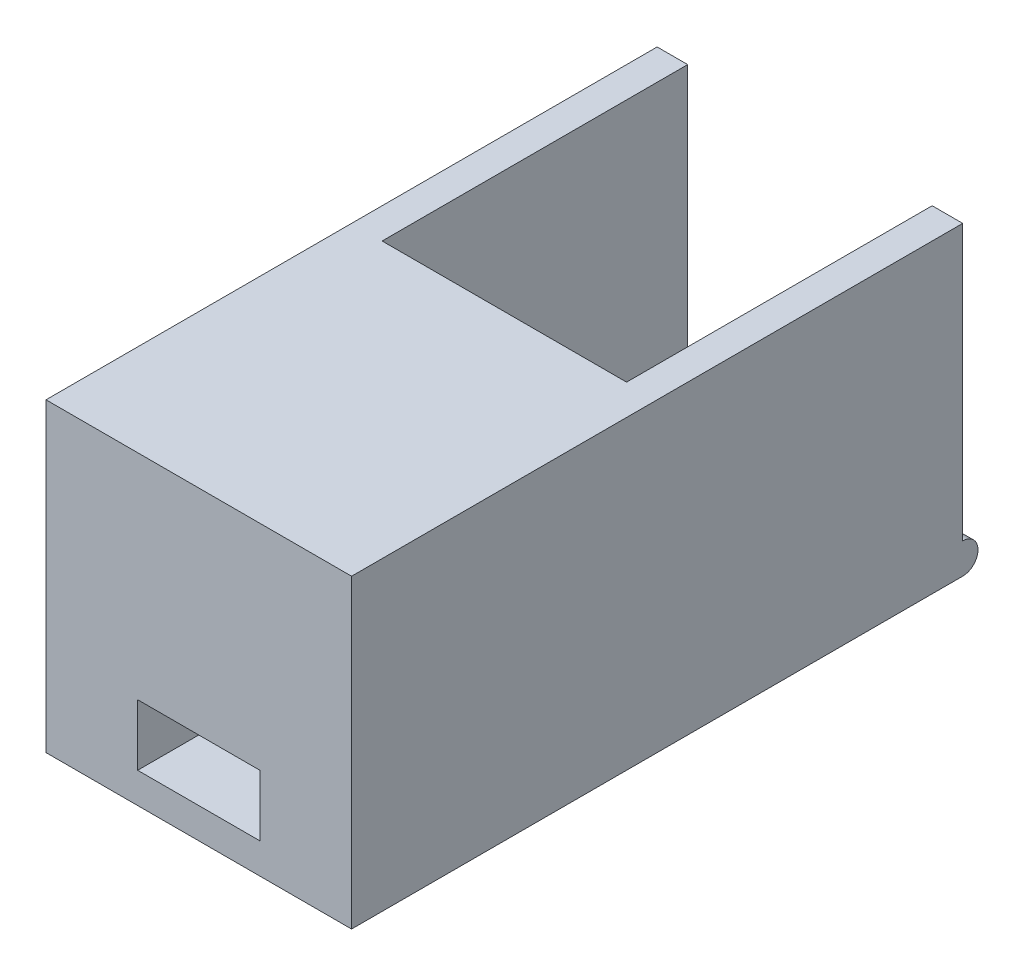
SolidWorks part; units mm, degrees
ref_plane "Front" through (0, 0, 0) normal (0, 0, 1) x (1, 0, 0)
ref_plane "Top" through (0, 0, 0) normal (0, 1, 0) x (1, 0, 0)
ref_plane "Right" through (0, 0, 0) normal (1, 0, 0) x (0, 0, -1)
sketch "草图1" plane through (0, 0, 0) normal (0, 1, 0) x (1, 0, 0)
  line L1 (-10, 20) -> (10, 20)
  line L2 (-10, 20) -> (-10, -20)
  line L3 (-10, -20) -> (10, -20)
  line L4 (10, 20) -> (10, -20)
  dimension "D1" = 40
  dimension "D2" = 20
  dimension "D3" = 10
  dimension "D4" = 20
extrude "凸台-拉伸1" add sketch "草图1" along normal blind 20
sketch "草图2" plane through (0, 20, 0) normal (0, 1, 0) x (1, 0, 0)
  line L0 (10, 20) -> (-10, 20) construction
  line L1 (-8, 20) -> (8, 20)
  line L2 (-8, 20) -> (-8, 0)
  line L3 (-8, 0) -> (8, 0)
  line L4 (8, 20) -> (8, 0)
  dimension "D1" = 16
  dimension "D2" = 8
extrude "切除-拉伸1" cut sketch "草图2" against normal blind 18
sketch "草图3" plane through (0, 0, 0) normal (0, -1, 0) x (1, 0, 0)
  line L0 (10, -20) -> (-10, -20) construction
  line L1 (-4, -42.4027) -> (4, -42.4027)
  line L2 (-4, -42.4027) -> (-4, -4)
  line L3 (-4, -4) -> (4, -4)
  line L4 (4, -42.4027) -> (4, -4)
  dimension "D1" = 8
  dimension "D2" = 4
  dimension "D3" = 16
extrude "切除-拉伸2" cut sketch "草图3" against normal blind 20
sketch "草图4" plane through (-4, 0, 0) normal (1, 0, 0) x (0, 0, -1)
  line L0 (20, 2) -> (20, 0) construction
  circle A0 centre (20, 1) radius 1
extrude "凸台-拉伸2" add sketch "草图4" against normal blind 6
sketch "草图5" plane through (4, 0, 0) normal (-1, 0, 0) x (0, 0, 1)
  line L0 (-20, 0) -> (-20, 2) construction
  circle A0 centre (-20, 1) radius 1
extrude "凸台-拉伸3" add sketch "草图5" against normal blind 6
sketch "草图6" plane through (0, 0, 0) normal (0, 0, -1) x (-1, 0, 0)
  line L1 (-4, 2) -> (4, 2)
  line L2 (-4, 2) -> (-4, 6)
  line L3 (-4, 6) -> (4, 6)
  line L4 (4, 2) -> (4, 6)
  dimension "D1" = 8
  dimension "D2" = 4
extrude "切除-拉伸3" cut sketch "草图6" against normal blind 30
